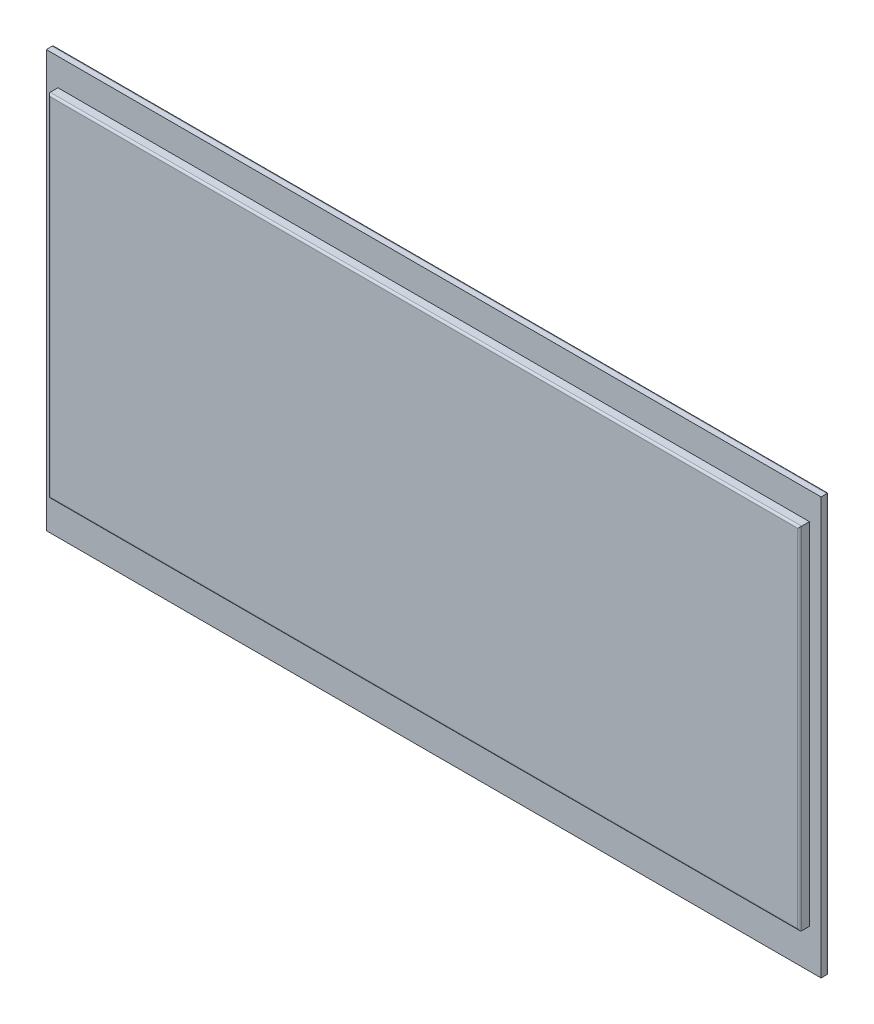
SolidWorks part; units mm, degrees
ref_plane "Front Plane" through (0, 0, 0) normal (0, 0, 1) x (1, 0, 0)
ref_plane "Top Plane" through (0, 0, 0) normal (0, 1, 0) x (1, 0, 0)
ref_plane "Right Plane" through (0, 0, 0) normal (1, 0, 0) x (0, 0, -1)
sketch "Sketch1" plane through (0, 0, 0) normal (0, 0, 1) x (1, 0, 0)
  line L1 (-99.5, -53.5) -> (99.5, -53.5)
  line L2 (-99.5, -53.5) -> (-99.5, 53.5)
  line L3 (-99.5, 53.5) -> (99.5, 53.5)
  line L4 (99.5, -53.5) -> (99.5, 53.5)
  line L5 (-99.5, -53.5) -> (99.5, 53.5) construction
  line L6 (-99.5, 53.5) -> (99.5, -53.5) construction
  point P0 (0, 0)
  dimension "D1" = 107
  dimension "D2" = 199
extrude "Boss-Extrude1" add sketch "Sketch1" along normal blind 2
sketch "Sketch2" plane through (0, 0, 2) normal (0, 0, 1) x (1, 0, 0)
  line L1 (-96.5, 46.5) -> (96.5, 46.5)
  line L2 (-96.5, 46.5) -> (-96.5, -43.5)
  line L3 (-96.5, -43.5) -> (96.5, -43.5)
  line L4 (96.5, 46.5) -> (96.5, -43.5)
  line L5 (99.5, -53.5) -> (99.5, 53.5) construction
  line L6 (-99.5, 53.5) -> (-99.5, -53.5) construction
  line L8 (99.5, 53.5) -> (-99.5, 53.5) construction
  dimension "D1" = 7
  dimension "D2" = 90
  dimension "D3" = 3
  dimension "D4" = 3
extrude "Boss-Extrude2" add sketch "Sketch2" along normal blind 2.5
fillet "Fillet2" radius 0.5 4 edges at (0, 46.5, 4.5) (96.5, 1.5, 4.5) (0, -43.5, 4.5) (-96.5, 1.5, 4.5)
fillet "Fillet3" radius 0.5 4 edges at (0, 53.5, 0) (-99.5, 0, 0) (0, -53.5, 0) (99.5, 0, 0)
